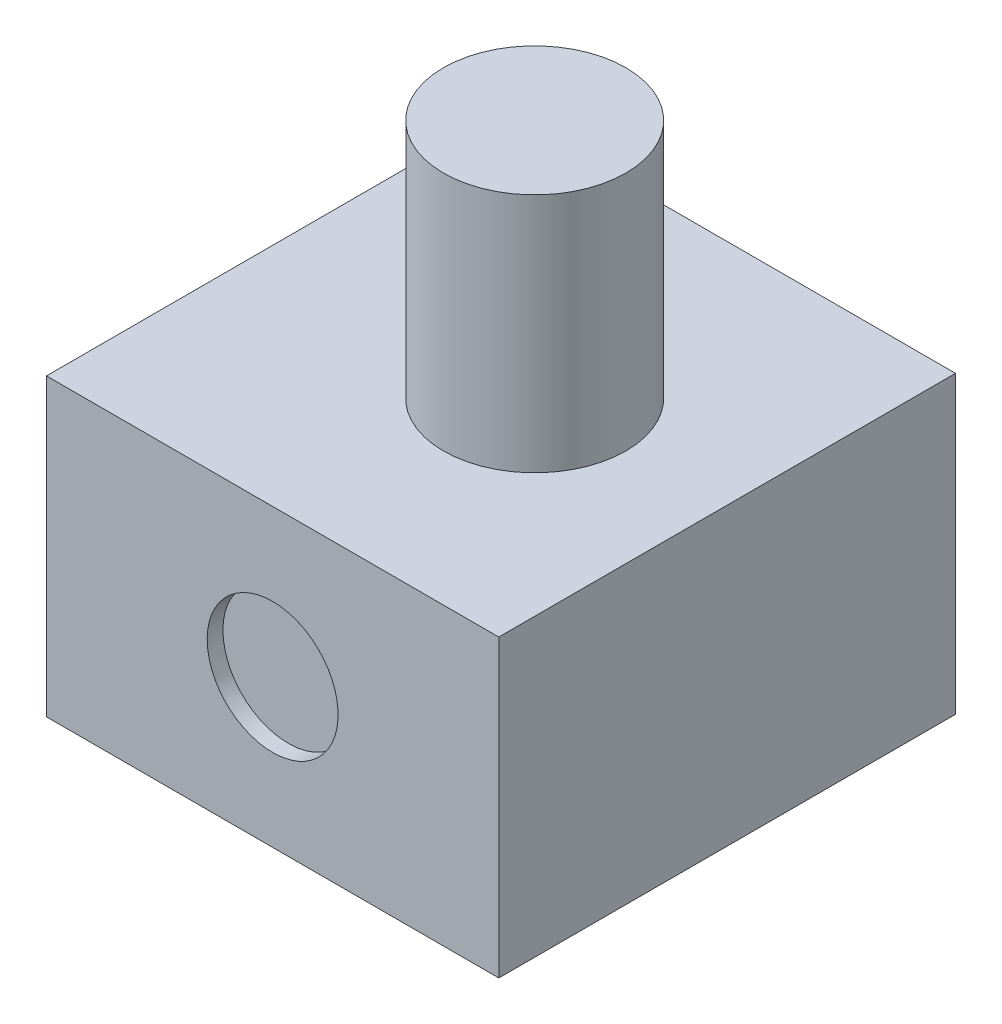
SolidWorks part; units mm, degrees
ref_plane "Front Plane" through (0, 0, 0) normal (0, 0, 1) x (1, 0, 0)
ref_plane "Top Plane" through (0, 0, 0) normal (0, 1, 0) x (1, 0, 0)
ref_plane "Right Plane" through (0, 0, 0) normal (1, 0, 0) x (0, 0, -1)
sketch "Sketch1" plane through (0, 0, 0) normal (0, 1, 0) x (1, 0, 0)
  line L1 (0, 0) -> (73.025, 0)
  line L2 (0, 0) -> (0, -73.7362)
  line L3 (0, -73.7362) -> (73.025, -73.7362)
  line L4 (73.025, 0) -> (73.025, -73.7362)
  dimension "D1" = 73.025
  dimension "D2" = 73.7362
extrude "Boss-Extrude1" add sketch "Sketch1" along normal blind 47.6758
sketch "Sketch2" plane through (0, 0, 0) normal (0, 0, -1) x (-1, 0, 0)
  line L0 (-73.025, 0) -> (0, 0) construction
  line L1 (-73.025, 47.6758) -> (-73.025, 0) construction
  circle A0 centre (-36.5125, 23.8379) radius 10.5664
  point P4 (-36.5125, 0)
  point P7 (-73.025, 23.8379)
  dimension "D1" = 21.1328
extrude "Cut-Extrude1" cut sketch "Sketch2" against normal blind 2.54
sketch "Sketch3" plane through (0, 47.6758, 0) normal (0, 1, 0) x (1, 0, 0)
  line L0 (73.025, 0) -> (0, 0) construction
  line L1 (73.025, -73.7362) -> (73.025, 0) construction
  circle A0 centre (42.545, -37.465) radius 14.732
  dimension "D1" = 29.464
  dimension "D2" = 37.465
  dimension "D3" = 30.48
extrude "Boss-Extrude2" add sketch "Sketch3" along normal blind 38.862
ref_plane "Plane1" through (0, 0, 36.8681) normal (0, 0, 1) x (1, 0, 0)
mirror "Mirror1" about plane through (0, 0, 36.8681) normal (0, 0, 1) of "Cut-Extrude1"
